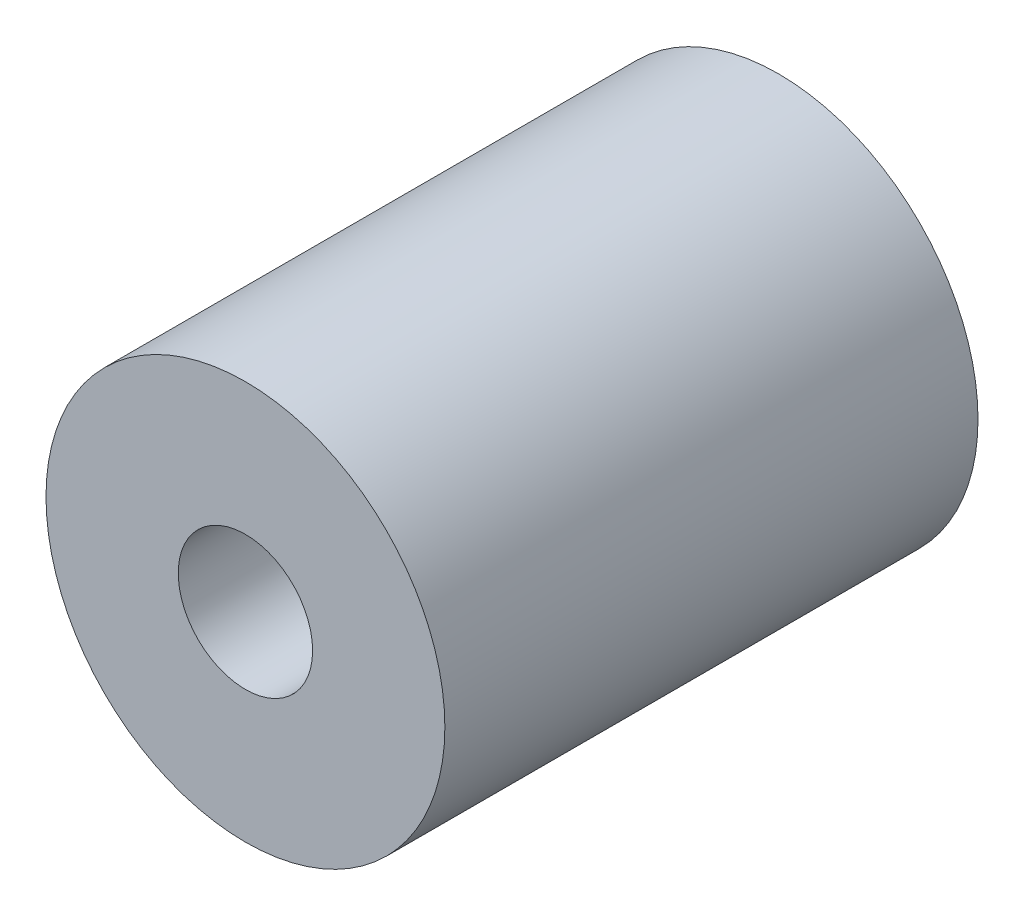
SolidWorks part; units mm, degrees
material "RBAR,1018CR"
ref_plane "Front Plane" through (0, 0, 0) normal (0, 0, 1) x (1, 0, 0)
ref_plane "Top Plane" through (0, 0, 0) normal (0, 1, 0) x (1, 0, 0)
ref_plane "Right Plane" through (0, 0, 0) normal (1, 0, 0) x (0, 0, -1)
sketch "Sketch1" plane through (0, 0, 0) normal (0, 0, 1) x (1, 0, 0)
  circle A0 centre (0, 0) radius 5.08
  circle A1 centre (0, 0) radius 15.0813
  dimension "D1" = 30.1625
  dimension "D2" = 10.16
extrude "Boss-Extrude1" add sketch "Sketch1" along normal blind 40.3162
